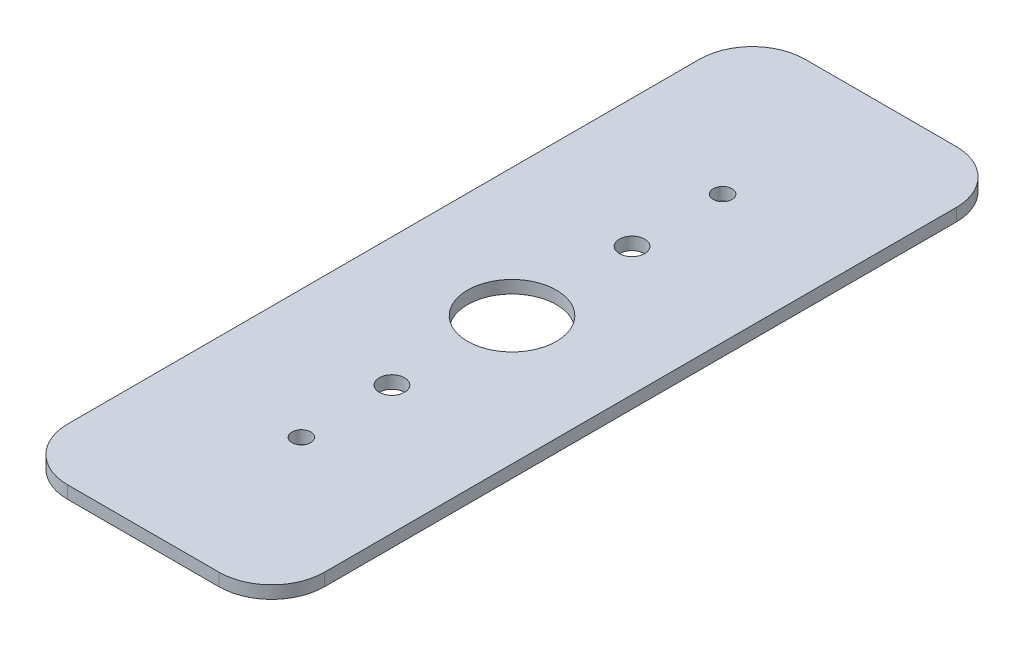
SolidWorks part; units mm, degrees
material "Acrylic (Medium-high impact)"
ref_plane "Front Plane" through (0, 0, 0) normal (0, 0, 1) x (1, 0, 0)
ref_plane "Top Plane" through (0, 0, 0) normal (0, 1, 0) x (1, 0, 0)
ref_plane "Right Plane" through (0, 0, 0) normal (1, 0, 0) x (0, 0, -1)
sketch "Sketch1" plane through (0, 0, 0) normal (0, 1, 0) x (1, 0, 0)
  line L0 (-15.4781, -44.45) -> (-15.4781, 44.45)
  line L1 (15.4781, 44.45) -> (15.4781, -44.45)
  line L2 (-15.4781, 0) -> (15.4781, 0) construction
  line L3 (0, 41.275) -> (0, -41.275) construction
  line L4 (-15.4781, 44.45) -> (15.4781, 44.45)
  line L5 (-15.4781, -44.45) -> (15.4781, -44.45)
  dimension "D2" = 30.9562
  dimension "D1" = 88.9
extrude "Boss-Extrude1" add sketch "Sketch1" along normal blind 1.524
fillet "Fillet1" radius 6.35 4 edges at (15.4781, 0.762, -44.45) (-15.4781, 0.762, -44.45) (15.4781, 0.762, 44.45) (-15.4781, 0.762, 44.45)
sketch "Sketch6" plane through (0, 0, 0) normal (0, -1, 0) x (1, 0, 0)
  line L0 (0, 0) -> (-28.2073, 0) construction
  line L1 (-9.1281, 44.45) -> (9.1281, 44.45) construction
  circle A0 centre (0, 14.478) radius 1.524
  circle A1 centre (0, -14.478) radius 1.524
  point P9 (0, 44.45)
  dimension "D1" = 3.048
  dimension "D2" = 14.478
extrude "Cut-Extrude1" cut sketch "Sketch6" against normal through all
hole_wizard "#4-40 Tapped Hole1" positions "Sketch5" profile "Sketch4" tap size "#4-40" standard "Ansi Inch" end condition through all
sketch "Sketch5" plane through (0, 1.524, 0) normal (0, 1, 0) x (-1, 0, 0)
  line L0 (0, 0) -> (16.1552, 0) construction
  point P0 (0, 25.4)
  point P9 (0, -25.4)
  dimension "D1" = 50.8
sketch "Sketch4" plane through (0, 1.524, 25.4) normal (1, 0, 0) x (0, 0, 1)
  line L0 (0, 0) -> (0, 1.524)
  line L1 (0, 1.524) -> (1.1303, 1.524)
  line L2 (1.1303, 1.524) -> (1.1303, 0)
  line L5 (1.1303, 0) -> (0, 0)
  line L11 (0, -6.35) -> (0, 107.95) construction
  dimension "Thread Major Dia." = 2.2606
  dimension "Thru Tap Drill Depth" = 1.524
hole_wizard "1/2-13 Tapped Hole1" positions "Sketch8" profile "Sketch7" tap size "1/2-13" standard "Ansi Inch" end condition through all
sketch "Sketch8" plane through (0, 1.524, 0) normal (0, 1, 0) x (-1, 0, 0)
  point P1 (0, 0)
sketch "Sketch7" plane through (0, 1.524, 0) normal (1, 0, 0) x (0, 0, 1)
  line L0 (0, 0) -> (0, 1.524)
  line L1 (0, 1.524) -> (5.3581, 1.524)
  line L2 (5.3581, 1.524) -> (5.3581, 0)
  line L5 (5.3581, 0) -> (0, 0)
  line L11 (0, -6.35) -> (0, 107.95) construction
  dimension "Thru Tap Drill Dia." = 10.7163
  dimension "Thru Tap Drill Depth" = 1.524
cosmetic thread "Hole Thread1" parameters "D2"=12.7
